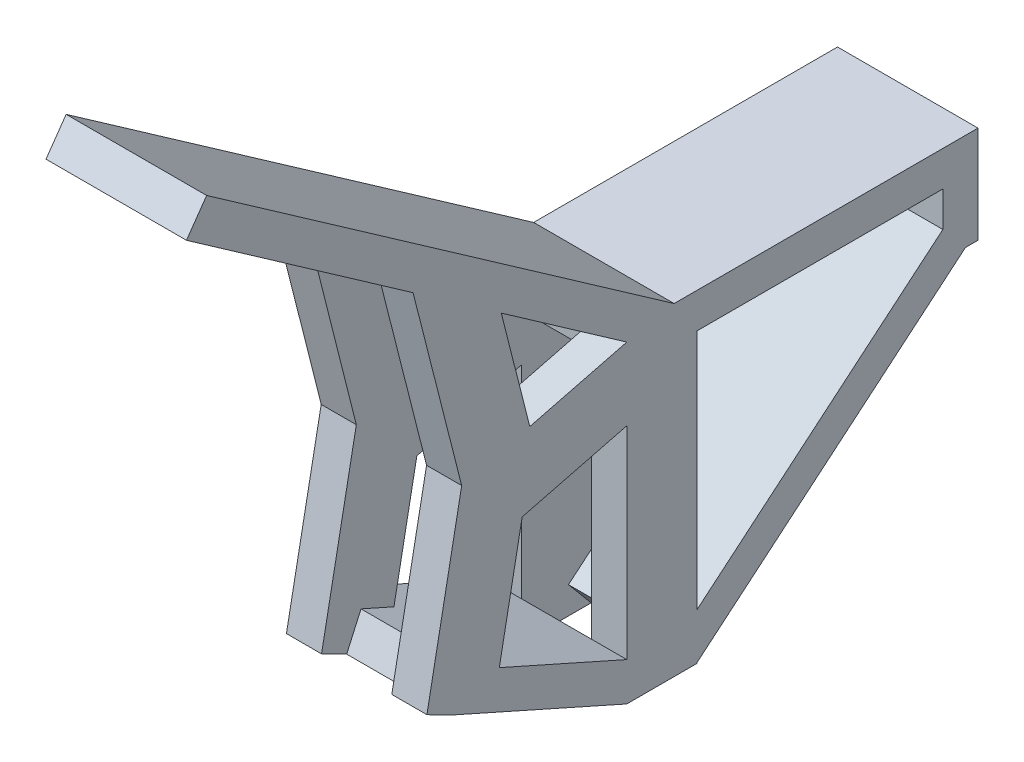
SolidWorks part; units mm, degrees
ref_plane "Спереди" through (0, 0, 0) normal (0, 0, 1) x (1, 0, 0)
ref_plane "Сверху" through (0, 0, 0) normal (0, 1, 0) x (1, 0, 0)
ref_plane "Справа" through (0, 0, 0) normal (1, 0, 0) x (0, 0, -1)
sketch "Эскиз1" plane through (0, 0, 0) normal (0, 0, 1) x (1, 0, 0)
  line L0 (-38.2906, 40) -> (-38.2906, 0)
  line L1 (-38.2906, 40) -> (121.7094, 40)
  line L2 (-38.2906, 0) -> (121.7094, 0)
  line L3 (121.7094, 40) -> (121.7094, 0)
  dimension "D1" = 40
  dimension "D2" = 160
extrude "Бобышка-Вытянуть1" add sketch "Эскиз1" along normal blind 400
sketch "Эскиз2" plane through (0, 40, 0) normal (0, 1, 0) x (1, 0, 0)
  line L0 (-38.2906, 0) -> (-38.2906, -400)
  line L1 (-38.2906, -400) -> (-38.2906, 0) construction
  dimension "D1" = 400
sketch "Эскиз8" plane through (-38.2906, 0, 0) normal (-1, 0, 0) x (0, 0, 1)
  line L0 (21.0535, 28.4928) -> (0, 40)
  line L1 (0, 40) -> (346.0806, 40)
  line L2 (0, 40) -> (400, 40) construction
  line L3 (346.0806, 40) -> (403.4053, 80.1392)
  line L4 (403.4053, 80.1392) -> (346.0806, 40)
  line L5 (346.0806, 40) -> (369.0236, 7.2339)
  line L6 (346.0806, 40) -> (369.0236, 7.2339)
  line L7 (346.0806, 40) -> (878.5294, 412.8247)
  line L8 (369.0236, 7.2339) -> (901.4725, 380.0586)
  line L9 (878.5294, 412.8247) -> (901.4725, 380.0586)
  line M7 (400, 0) -> (400, 40)
  line M8 (400, 40) -> (0, 40)
  dimension "D1" = 346.0806
  dimension "D2" = 90
  dimension "D3" = 35
  dimension "D4" = 40
  dimension "D5" = 650
extrude "Бобышка-Вытянуть6" add sketch "Эскиз8" against normal blind 160 contours L9 L7 L3 L8 M8 M7
sketch "Эскиз11" plane through (-38.2906, 0, 0) normal (-1, 0, 0) x (0, 0, 1)
  line L0 (901.4725, 380.0586) -> (717.1632, 251.0039)
  line L1 (400, 28.9238) -> (901.4725, 380.0586) construction
  line L2 (0, 0) -> (0, -40)
  line L3 (711.0272, 151.908) -> (650.7362, 204.4912)
  line L4 (711.0272, 151.908) -> (415.2464, -187.2288)
  line L5 (650.7362, 204.4912) -> (354.9554, -134.6455)
  line L6 (415.2464, -187.2288) -> (354.9554, -134.6455)
  line L7 (0, 0) -> (40, 0)
  line L8 (0, -40) -> (40, -40)
  line L9 (40, 0) -> (40, -40)
  line M10 (0, 0) -> (400, 0)
  dimension "D1" = 225
  dimension "D2" = 80
  dimension "D3" = 40
  dimension "D4" = 450
  dimension "D5" = 40
extrude "Бобышка-Вытянуть7" add sketch "Эскиз11" against normal blind 160 contours L9 L2 L8 M10
sketch "Эскиз12" plane through (-38.2906, 0, 0) normal (-1, 0, 0) x (0, 0, 1)
  line L0 (40, 0) -> (40, -40) construction
  line L1 (40, -40) -> (346.4178, -297.115)
  line L2 (40, -40) -> (14.2885, -70.6418)
  line L3 (14.2885, -70.6418) -> (40, -40)
  line L4 (14.2885, -70.6418) -> (320.7063, -327.7568)
  line L5 (40, -40) -> (346.4178, -297.115)
  line L6 (320.7063, -327.7568) -> (346.4178, -297.115)
  line L7 (14.2885, -70.6418) -> (0, -70.6418)
  line L8 (0, -70.6418) -> (0, -40)
  dimension "D1" = 400
  dimension "D2" = 130
  dimension "D3" = 40
extrude "Бобышка-Вытянуть11" add sketch "Эскиз12" against normal blind 160 contours L4 L6 L1 L2 | L8 L7 L2 L5
sketch "Эскиз17" plane through (0, 0, 0) normal (0, -1, 0) x (-1, 0, 0)
  line L0 (38.2906, -400) -> (-1.7094, -400)
  line L1 (38.2906, -400) -> (38.2906, -320)
  line L2 (-1.7094, -400) -> (-1.7094, -320)
  line L3 (38.2906, -320) -> (-1.7094, -320)
  line L4 (38.2906, -400) -> (-121.7094, -400) construction
  line L5 (-121.7094, -400) -> (-81.7094, -400)
  line L6 (-121.7094, -400) -> (-121.7094, -320)
  line L7 (-81.7094, -400) -> (-81.7094, -320)
  line L8 (-121.7094, -320) -> (-81.7094, -320)
  dimension "D1" = 80
  dimension "D2" = 80
  dimension "D3" = 40
  dimension "D4" = 40
extrude "Бобышка-Вытянуть13" add sketch "Эскиз17" along normal blind 328
sketch "Эскиз19" plane through (0, 0, 400) normal (0, 0, 1) x (1, 0, 0)
  line L0 (1.7094, 0) -> (1.7094, 28.9238)
  line L1 (121.7094, 28.9238) -> (-38.2906, 28.9238) construction
  line L2 (81.7094, 0) -> (81.7094, 28.9238)
  line L3 (1.7094, 0) -> (21.7094, 0)
  line L4 (1.7094, 0) -> (81.7094, 0) construction
  line L6 (21.7094, 0) -> (61.7094, 0)
  line L7 (21.7094, 0) -> (21.7094, 28.9238)
  line L8 (21.7094, 28.9238) -> (61.7094, 28.9238)
  line L9 (61.7094, 0) -> (61.7094, 28.9238)
  line L10 (21.7094, 28.9238) -> (31.7094, 28.9238)
  line L11 (21.7094, 28.9238) -> (21.7094, 0)
  line L12 (21.7094, 0) -> (31.7094, 0)
  line L13 (31.7094, 28.9238) -> (31.7094, 0)
  line L14 (61.7094, 0) -> (51.7094, 0)
  line L15 (61.7094, 0) -> (61.7094, 28.9238)
  line L16 (61.7094, 28.9238) -> (51.7094, 28.9238)
  line L17 (51.7094, 0) -> (51.7094, 28.9238)
  dimension "D1" = 20
  dimension "D2" = 40
  dimension "D3" = 10
  dimension "D4" = 10
sketch "Эскиз26" plane through (-38.2906, 0, 0) normal (-1, 0, 0) x (0, 0, 1)
  line L0 (400, -328) -> (400, -284.2145)
  line L1 (400, 28.9238) -> (400, -328) construction
  line L2 (400, -284.2145) -> (416.2695, -320.7564)
  line L3 (400, -284.2145) -> (416.2695, -320.7564)
  line L4 (400, -284.2145) -> (582.7091, -202.8672)
  line L5 (416.2695, -320.7564) -> (598.9786, -239.409)
  line L6 (582.7091, -202.8672) -> (598.9786, -239.409)
  line L7 (416.2695, -320.7564) -> (400, -328)
  line M7 (400, -328) -> (400, 28.9238)
  dimension "D1" = 24
  dimension "D2" = 40
  dimension "D4" = 200
extrude "Бобышка-Вытянуть17" add sketch "Эскиз26" against normal blind 160 contours L7 L2 M7 | L6 L4 L2 L5
sketch "Эскиз27" plane through (-38.2906, 0, 0) normal (-1, 0, 0) x (0, 0, 1)
  line L0 (582.7091, -202.8672) -> (598.9786, -239.409)
  line L1 (598.9786, -239.409) -> (582.7091, -202.8672)
  line L2 (549.0842, -239.8721) -> (627.6488, -224.7858)
  line L3 (549.0842, -239.8721) -> (537.7694, -180.9487)
  line L4 (627.6488, -224.7858) -> (616.334, -165.8623)
  line L5 (537.7694, -180.9487) -> (616.334, -165.8623)
  line L6 (549.0842, -239.8721) -> (616.334, -165.8623) construction
  line L7 (627.6488, -224.7858) -> (537.7694, -180.9487) construction
  line L8 (537.7694, -180.9487) -> (616.334, -165.8623)
  line L9 (537.7694, -180.9487) -> (509.4825, -33.64)
  line L10 (616.334, -165.8623) -> (588.0471, -18.5536)
  line L11 (509.4825, -33.64) -> (588.0471, -18.5536)
  line L12 (627.6488, -224.7858) -> (598.9786, -239.409)
  line L13 (598.9786, -239.409) -> (549.0842, -239.8721)
  line M10 (598.9786, -239.409) -> (582.7091, -202.8672)
  line M11 (582.7091, -202.8672) -> (400, -284.2145)
  dimension "D1" = 80
  dimension "D2" = 60
  dimension "D3" = 40
  dimension "D4" = 150
extrude "Бобышка-Вытянуть18" add sketch "Эскиз27" against normal blind 40 contours L11 L9 L5 L10 | L5 L3 L1 L2 L4 M11 | L12 L2 M10
sketch "Эскиз28" plane through (121.7094, 0, 0) normal (1, 0, 0) x (0, 0, -1)
  line L0 (-598.9786, -239.409) -> (-582.7091, -202.8672)
sketch "Эскиз29" plane through (0, 108.2442, 563.6988) normal (0, 0.1886, 0.9821) x (1, 0, 0)
  line L0 (-38.2906, -129.1144) -> (-38.2906, -339.1144)
  line L1 (-38.2906, -129.1144) -> (121.7094, -129.1144)
  line L2 (-38.2906, -339.1144) -> (121.7094, -339.1144)
  line L3 (121.7094, -129.1144) -> (121.7094, -339.1144)
  line L5 (121.7094, -129.1144) -> (81.7094, -129.1144)
  line L6 (121.7094, -129.1144) -> (121.7094, -339.1144)
  line L7 (121.7094, -339.1144) -> (81.7094, -339.1144)
  line L8 (81.7094, -129.1144) -> (81.7094, -339.1144)
  dimension "D1" = 160
  dimension "D2" = 40
extrude "Бобышка-Вытянуть19" add sketch "Эскиз29" against normal blind 80 contours L1 L8 L2 L3
sketch "Эскиз33" plane through (121.7094, 0, 0) normal (1, 0, 0) x (0, 0, -1)
  line L0 (-627.6488, -224.7858) -> (-598.9786, -239.409)
  line L1 (-598.9786, -239.409) -> (-595.2388, -231.0093)
  line L2 (-595.2388, -231.0093) -> (-627.6488, -224.7858)
extrude "Бобышка-Вытянуть20" add sketch "Эскиз33" against normal blind 40
sketch "Эскиз34" plane through (-38.2906, 0, 0) normal (-1, 0, 0) x (0, 0, 1)
  line L0 (490.8975, -76.536) -> (510.4811, 1.03)
  line L1 (510.4811, 1.03) -> (588.0471, -18.5536)
  line L2 (588.0471, -18.5536) -> (490.8975, -76.536)
  line L3 (510.4811, 1.03) -> (490.8975, -76.536)
  line L4 (510.4811, 1.03) -> (400, 28.9238)
  line L5 (490.8975, -76.536) -> (380.4164, -48.6422)
  line L6 (400, 28.9238) -> (380.4164, -48.6422)
  line L7 (510.4811, 1.03) -> (588.0471, -18.5536)
  line L8 (510.4811, 1.03) -> (565.4255, 218.6518)
  line L9 (588.0471, -18.5536) -> (642.9914, 199.0683)
  line L10 (565.4255, 218.6518) -> (642.9914, 199.0683)
  line L14 (400, 28.9238) -> (901.4725, 380.0586) construction
  line L16 (400, 28.9238) -> (400, -284.2145) construction
  line L19 (490.8975, -76.536) -> (519.0862, -83.653)
  line L20 (545.1863, -219.5734) -> (509.4825, -33.64) construction
  line M3 (509.4825, -33.64) -> (545.1863, -219.5734)
  line M5 (400, -284.2145) -> (400, 28.9238)
  line M6 (400, 28.9238) -> (901.4725, 380.0586)
  line M18 (588.0471, -18.5536) -> (509.4825, -33.64)
  dimension "D1" = 80
  dimension "D2" = 80
  dimension "D3" = 180
  dimension "D4" = 180
extrude "Бобышка-Вытянуть21" add sketch "Эскиз34" against normal blind 40 contours L5 L0 L4 M5 | L2 L1 L0 M3 M18 | L2 L19 M3 | L1 L9 L8 M6
sketch "Эскиз35" plane through (121.7094, 0, 0) normal (1, 0, 0) x (0, 0, -1)
  line L0 (-588.0471, -18.5536) -> (-643.4236, 199.3709)
  line L1 (-400, 28.9238) -> (-901.4725, 380.0586) construction
  line L2 (-643.4236, 199.3709) -> (-543.0157, 129.0645)
  line L3 (-543.0157, 129.0645) -> (-510.438, 0.8606)
  line L4 (-510.438, 0.8606) -> (-400, 28.9238)
  line L5 (-400, 28.9238) -> (-400, -53.6186)
  line L6 (-400, -284.2145) -> (-400, 28.9238) construction
  line L7 (-400, -53.6186) -> (-519.1319, -83.8911)
  line L8 (-509.4825, -33.64) -> (-545.1863, -219.5734) construction
  line L9 (-519.1319, -83.8911) -> (-509.4825, -33.64)
  line L10 (-509.4825, -33.64) -> (-588.0471, -18.5536)
  dimension "D1" = 80
  dimension "D2" = 90
  dimension "D3" = 80
extrude "Бобышка-Вытянуть22" add sketch "Эскиз35" against normal blind 40
